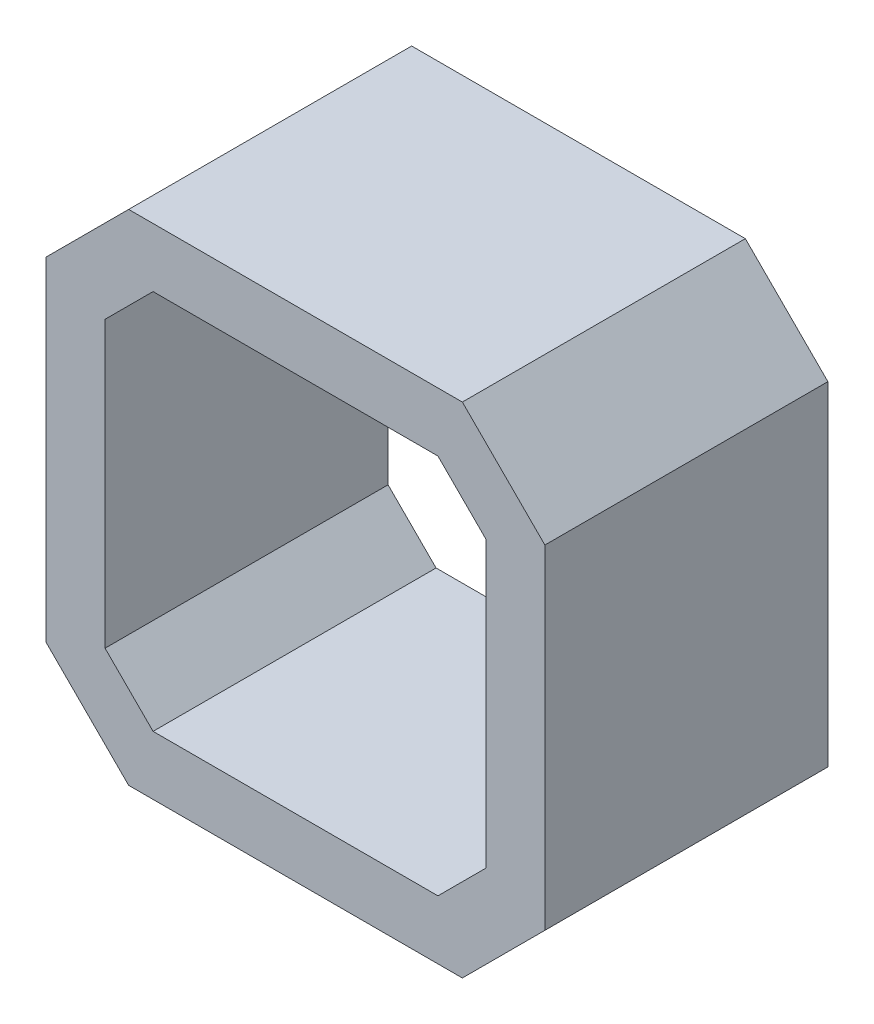
SolidWorks part; units mm, degrees
ref_plane "Front Plane" through (0, 0, 0) normal (0, 0, 1) x (1, 0, 0)
ref_plane "Top Plane" through (0, 0, 0) normal (0, 1, 0) x (1, 0, 0)
ref_plane "Right Plane" through (0, 0, 0) normal (1, 0, 0) x (0, 0, -1)
sketch "Sketch1" plane through (0, 0, 0) normal (0, 0, 1) x (1, 0, 0)
  line L0 (-42.3, 28.3) -> (-28.3, 42.3)
  line L1 (-28.3, -42.3) -> (28.3, -42.3)
  line L2 (-42.3, -28.3) -> (-42.3, 28.3)
  line L3 (-28.3, 42.3) -> (28.3, 42.3)
  line L4 (42.3, -28.3) -> (42.3, 28.3)
  line L5 (-42.3, -42.3) -> (42.3, 42.3) construction
  line L6 (-42.3, 42.3) -> (42.3, -42.3) construction
  line L7 (28.3, 42.3) -> (42.3, 28.3)
  line L8 (28.3, -42.3) -> (42.3, -28.3)
  line L9 (-42.3, -28.3) -> (-28.3, -42.3)
  line L10 (-24.1579, 32.3) -> (24.1579, 32.3)
  line L11 (24.1579, 32.3) -> (32.3, 24.1579)
  line L12 (32.3, -24.1579) -> (32.3, 24.1579)
  line L13 (24.1579, -32.3) -> (32.3, -24.1579)
  line L14 (-24.1579, -32.3) -> (24.1579, -32.3)
  line L15 (-32.3, -24.1579) -> (-24.1579, -32.3)
  line L16 (-32.3, -24.1579) -> (-32.3, 24.1579)
  line L17 (-32.3, 24.1579) -> (-24.1579, 32.3)
  point P0 (0, 0)
  dimension "D1" = 84.6
  dimension "D2" = 84.6
  dimension "D3" = 10
extrude "Boss-Extrude1" add sketch "Sketch1" along normal blind 48
